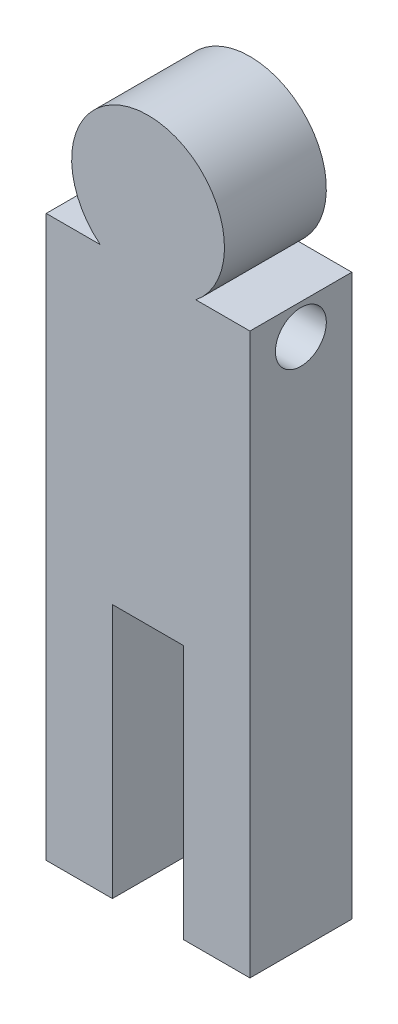
SolidWorks part; units mm, degrees
ref_plane "Alzado" through (0, 0, 0) normal (0, 0, 1) x (1, 0, 0)
ref_plane "Planta" through (0, 0, 0) normal (0, 1, 0) x (1, 0, 0)
ref_plane "Vista lateral" through (0, 0, 0) normal (1, 0, 0) x (0, 0, -1)
sketch "Croquis1" plane through (0, 0, 0) normal (0, 0, 1) x (1, 0, 0)
  line L0 (-10, -15) -> (-10, -40)
  line L1 (-3.5, -15) -> (3.5, -15)
  line L2 (-10, -15) -> (-10, 15)
  line L3 (-10, 15) -> (-4.6953, 15)
  line L4 (10, -15) -> (10, 15)
  line L5 (-10, -15) -> (10, 15) construction
  line L6 (-10, 15) -> (10, -15) construction
  line L7 (-10, -40) -> (-3.5, -40)
  line L8 (-3.5, -40) -> (-3.5, -15)
  line L9 (10, -15) -> (10, -40)
  line L10 (10, -40) -> (3.5, -40)
  line L11 (3.5, -40) -> (3.5, -15)
  line L12 (4.6953, 15) -> (10, 15)
  arc A0 (4.6953, 15) -> (-4.6953, 15) centre (0, 20.8484) ccw
  point P0 (0, 0)
  dimension "D7" = 15
  dimension "D1" = 20
  dimension "D2" = 30
  dimension "D3" = 6.5
  dimension "D4" = 6.5
  dimension "D5" = 25
  dimension "D6" = 25
extrude "Saliente-Extruir1" add sketch "Croquis1" along normal blind 10
sketch "Croquis2" plane through (10, 0, 0) normal (1, 0, 0) x (0, 0, -1)
  line L0 (-10, -40) -> (-10, 15) construction
  line L1 (-10, 15) -> (0, 15) construction
  circle A0 centre (-5, 12) radius 2.5
  dimension "D1" = 5
  dimension "D3" = 3
  dimension "D2" = 5
extrude "Cortar-Extruir1" cut sketch "Croquis2" against normal blind 21
